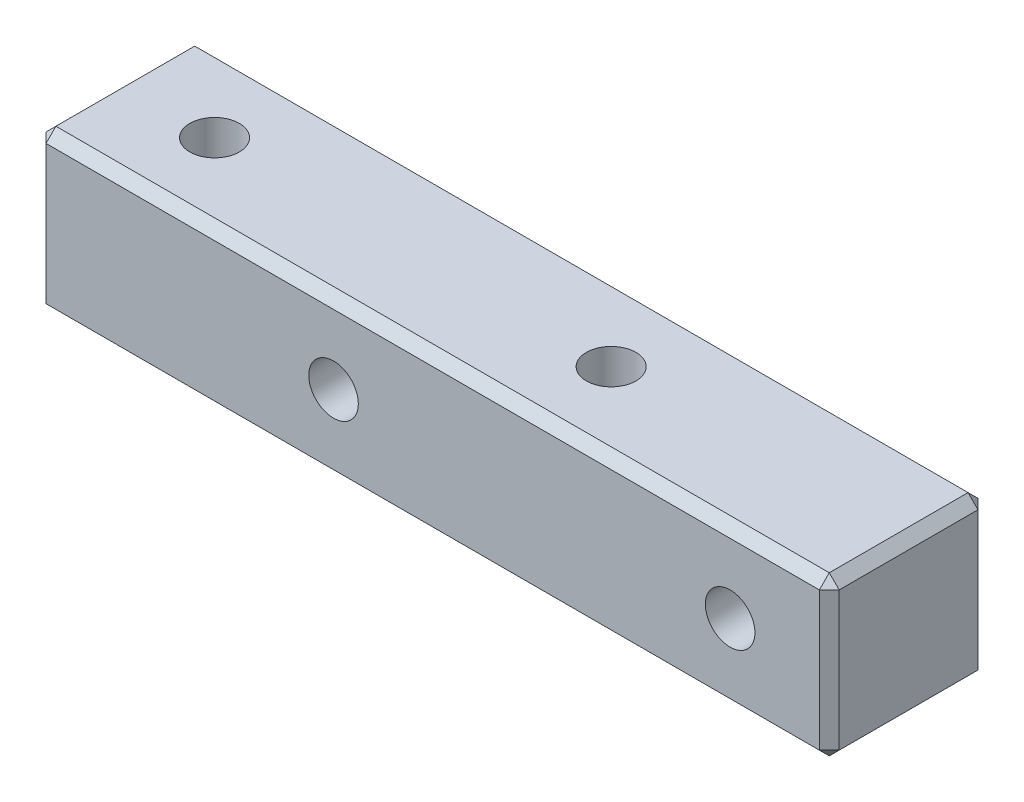
SolidWorks part; units mm, degrees
material "6061 合金"
ref_plane "前视基准面" through (0, 0, 0) normal (0, 0, 1) x (1, 0, 0)
ref_plane "上视基准面" through (0, 0, 0) normal (0, 1, 0) x (1, 0, 0)
ref_plane "右视基准面" through (0, 0, 0) normal (1, 0, 0) x (0, 0, -1)
sketch "草图2" plane through (0, 0, 0) normal (0, 0, 1) x (1, 0, 0)
  line L10 (5, 4) -> (5, -4)
  line L11 (0, 0) -> (-20, 0) construction
  line L41 (5, -4) -> (-35, -4)
  line L48 (-35, 4) -> (5, 4)
  line L49 (-35, 4) -> (-35, -4)
  circle A3 centre (-20, 0) radius 0.5
  circle A5 centre (0, 0) radius 0.5
  dimension "D1" = 20
  dimension "D2" = 1
  dimension "D3" = 4
  dimension "D4" = 15
  dimension "D7" = 5
  dimension "D6" = 4
extrude "凸台-拉伸1" add sketch "草图2" along normal mid plane 8
hole_wizard "M3 螺纹孔1" positions "草图5" profile "草图4" tap size "M3" standard "GB" end condition through all
sketch "草图5" plane through (0, 0, 4) normal (0, 0, 1) x (1, 0, 0)
  point P0 (0, 0)
  point P3 (-20, 0)
sketch "草图4" plane through (0, 0, 4) normal (1, 0, 0) x (0, -1, 0)
  line L0 (0, 0) -> (0, 8)
  line L1 (0, 8) -> (1.25, 8)
  line L2 (1.25, 8) -> (1.25, 0)
  line L5 (1.25, 0) -> (0, 0)
  line L11 (0, -6.35) -> (0, 107.95) construction
  dimension "通孔螺纹孔钻头直径" = 2.5
  dimension "通孔螺纹孔钻头深度" = 8
cosmetic thread "孔螺蚊线3" parameters "D2"=3
cosmetic thread "孔螺蚊线4" parameters "D2"=3
hole_wizard "M3 螺纹孔2" positions "草图6" profile "草图7" tap size "M3" standard "GB" end condition through all
sketch "草图6" plane through (0, 4, 0) normal (0, 1, 0) x (1, 0, 0)
  line L1 (-30, 0) -> (0, 0) construction
  line L2 (-35, -4) -> (-35, 4) construction
  point P0 (-10, 0)
  point P2 (-30, 0)
  dimension "D1" = 5
  dimension "D2" = 20
sketch "草图7" plane through (-10, 4, 0) normal (1, 0, 0) x (0, 0, 1)
  line L0 (0, 0) -> (0, 8)
  line L1 (0, 8) -> (1.25, 8)
  line L2 (1.25, 8) -> (1.25, 0)
  line L5 (1.25, 0) -> (0, 0)
  line L11 (0, -6.35) -> (0, 107.95) construction
  dimension "通孔螺纹孔钻头直径" = 2.5
  dimension "通孔螺纹孔钻头深度" = 8
cosmetic thread "孔螺蚊线5" parameters "D2"=3
cosmetic thread "孔螺蚊线6" parameters "D2"=3
chamfer "倒角1" distance 0.5 angle 45 12 edges at (-15, -4, -4) (-15, -4, 4) (-35, 0, -4) (-35, 0, 4) (5, -4, 0) (5, 0, 4) (5, 0, -4) (-15, 4, -4) (5, 4, 0) (-15, 4, 4) (-35, 4, 0) (-35, -4, 0)
